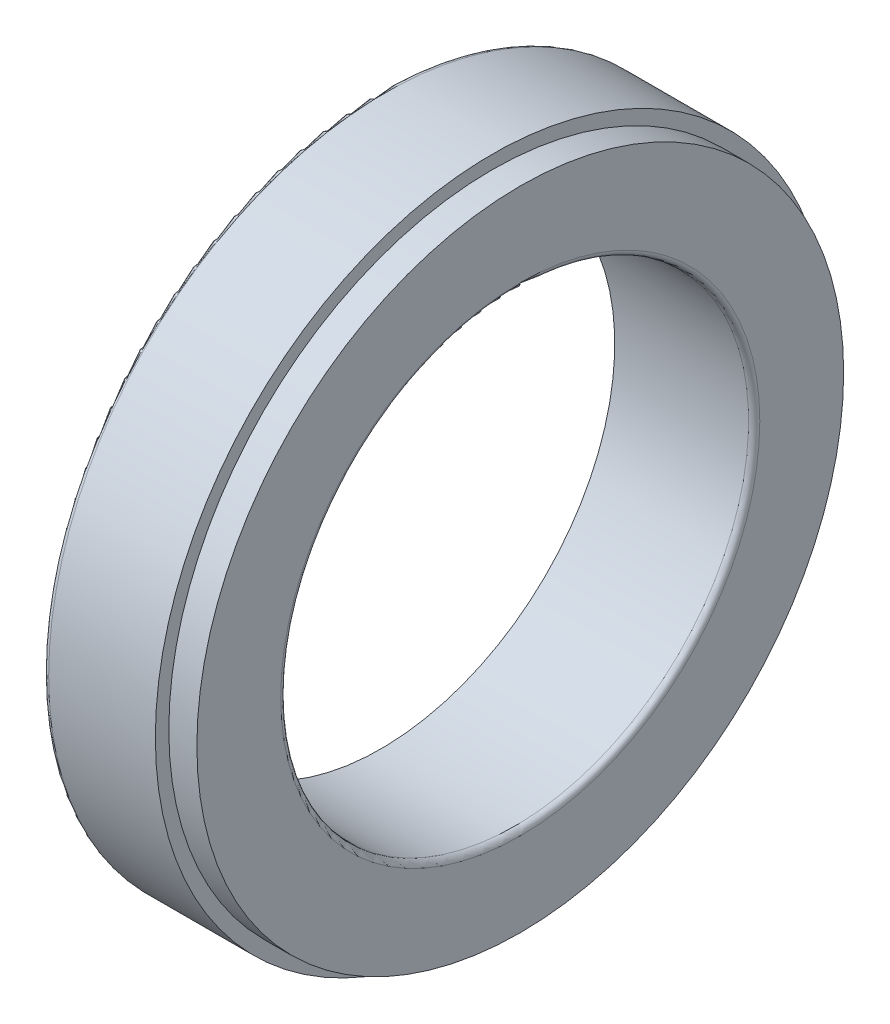
SolidWorks part; units mm, degrees
material "AISI 1020"
ref_plane "Спереди" through (0, 0, 0) normal (0, 0, 1) x (1, 0, 0)
ref_plane "Сверху" through (0, 0, 0) normal (0, 1, 0) x (1, 0, 0)
ref_plane "Справа" through (0, 0, 0) normal (1, 0, 0) x (0, 0, -1)
sketch "Эскиз1" plane through (0, 0, 0) normal (0, 0, 1) x (1, 0, 0)
  line L0 (-1000, 0) -> (49000, 0) construction
  line L2 (0.6, 36) -> (12, 36)
  line L3 (0, 35.4) -> (0, 31.374)
  line L4 (0.1, 25) -> (14.4, 25)
  line L5 (15, 34.561) -> (15, 25.6)
  line L7 (12, 36) -> (12, 34.561)
  line L8 (12, 34.561) -> (15, 34.561)
  line L10 (0.1, 31.374) -> (0.1, 25)
  line L11 (12, 34.561) -> (12, 31.374) construction
  line L12 (12, 31.374) -> (12, 28.187) construction
  line L13 (12, 28.187) -> (12, 25) construction
  line L14 (0, 31.374) -> (0.1, 31.374)
  arc A0 (14.4, 25) -> (15, 25.6) centre (14.4, 25.6) ccw
  arc A1 (0.6, 36) -> (0, 35.4) centre (0.6, 35.4) ccw
  dimension "_r1" = 0.6
  dimension "_r2" = 0.6
  dimension "_E" = 62.748
  dimension "_D" = 72
  dimension "_d_" = 50
  dimension "_B" = 14.9
  dimension "_C" = 12
  dimension "_T" = 15
revolve "Повернуть1" add sketch "Эскиз1" angle 360 about L0
